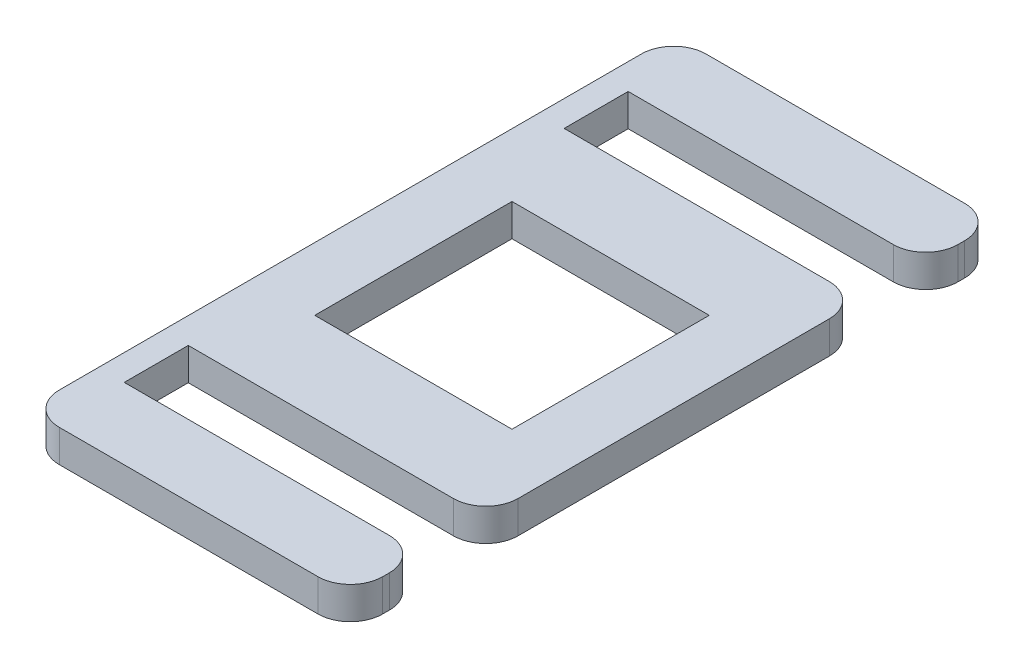
SolidWorks part; units mm, degrees
ref_plane "Front Plane" through (0, 0, 0) normal (0, 0, 1) x (1, 0, 0)
ref_plane "Top Plane" through (0, 0, 0) normal (0, 1, 0) x (1, 0, 0)
ref_plane "Right Plane" through (0, 0, 0) normal (1, 0, 0) x (0, 0, -1)
sketch "Sketch1" plane through (0, 0, 0) normal (0, 1, 0) x (1, 0, 0)
  line L1 (-25, -50) -> (25, -50)
  line L2 (-25, -50) -> (-25, 50)
  line L3 (-25, 50) -> (25, 50)
  line L4 (25, -50) -> (25, 50)
  line L5 (0, 50) -> (0, -50) construction
  line L6 (-25, 0) -> (25, 0) construction
  point P0 (0, 0)
  dimension "D1" = 50
  dimension "D2" = 100
extrude "Boss-Extrude1" add sketch "Sketch1" along normal blind 5
sketch "Sketch2" plane through (0, 5, 0) normal (0, 1, 0) x (1, 0, 0)
  line L0 (0, 50) -> (0, -50) construction
  line L1 (25, 50) -> (-25, 50) construction
  line L2 (-25, -50) -> (25, -50) construction
  line L6 (-21, -38.96) -> (31.8954, -38.96)
  line L7 (-21, -38.96) -> (-21, -29.06)
  line L8 (-21, -29.06) -> (31.8954, -29.06)
  line L9 (31.8954, -38.96) -> (31.8954, -29.06)
  line L10 (5.4477, -29.06) -> (5.4477, -38.96) construction
  line L11 (-21, -34.01) -> (31.8954, -34.01) construction
  point P6 (5.4477, -34.01)
  dimension "D2" = 9.9
  dimension "D1" = 34.01
  dimension "D3" = 21
extrude "Cut-Extrude1" cut sketch "Sketch2" against normal through all
mirror "Mirror1" about plane through (0, 0, 0) normal (0, 0, 1) of "Cut-Extrude1"
fillet "Fillet1" radius 5 8 edges at (25, 2.5, 38.96) (25, 2.5, 29.06) (25, 2.5, -29.06) (25, 2.5, -38.96) (25, 2.5, -50) (-25, 2.5, -50) (25, 2.5, 50) (-25, 2.5, 50)
sketch "Sketch3" plane through (0, 5, 0) normal (0, 1, 0) x (1, 0, 0)
  line L1 (-15.25, 15.25) -> (15.25, 15.25)
  line L2 (-15.25, 15.25) -> (-15.25, -15.25)
  line L3 (-15.25, -15.25) -> (15.25, -15.25)
  line L4 (15.25, 15.25) -> (15.25, -15.25)
  line L5 (0, -15.25) -> (0, 15.25) construction
  line L6 (-15.25, 0) -> (15.25, 0) construction
  point P0 (0, 0)
  dimension "D1" = 30.5
extrude "Cut-Extrude2" cut sketch "Sketch3" against normal through all
